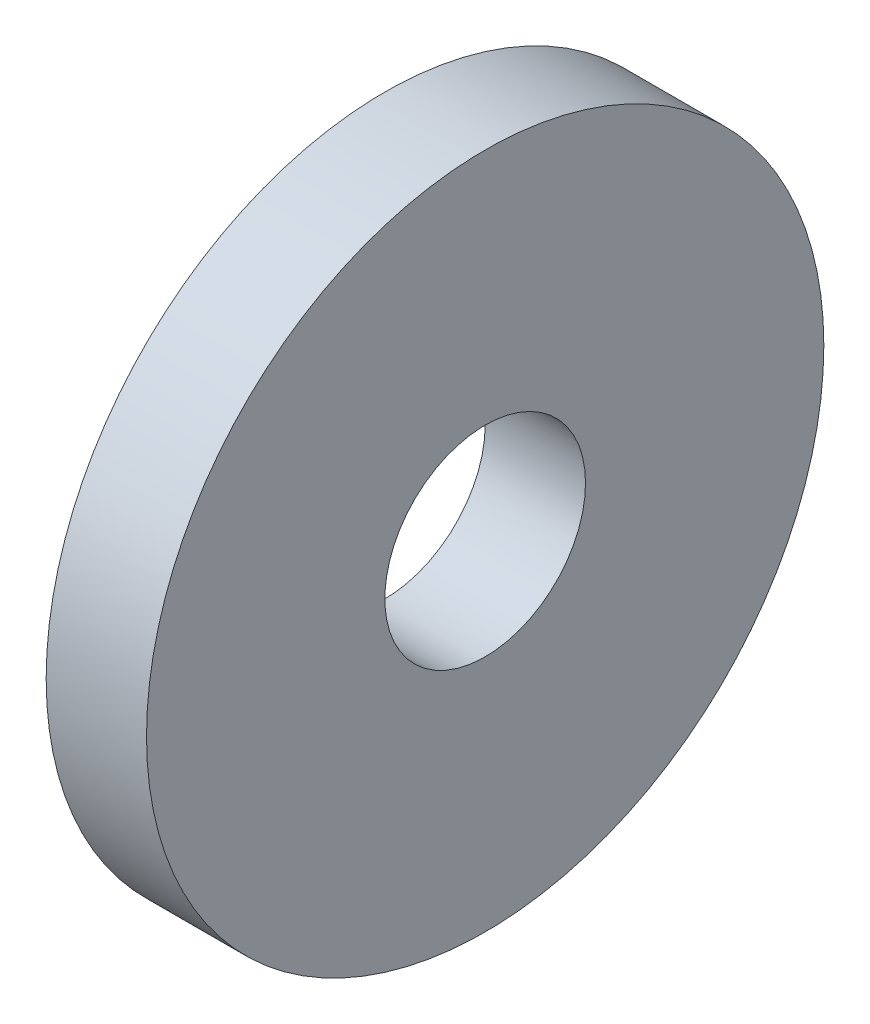
SolidWorks part; units mm, degrees
material "Pine"
ref_plane "Front Plane" through (0, 0, 0) normal (0, 0, 1) x (1, 0, 0)
ref_plane "Top Plane" through (0, 0, 0) normal (0, 1, 0) x (1, 0, 0)
ref_plane "Right Plane" through (0, 0, 0) normal (1, 0, 0) x (0, 0, -1)
sketch "Sketch1" plane through (0, 0, 0) normal (1, 0, 0) x (0, 0, -1)
  circle A0 centre (0, 0) radius 6.75
  dimension "D1" = 13.5
extrude "Boss-Extrude1" add sketch "Sketch1" along normal blind 2
sketch "Sketch2" plane through (2, 0, 0) normal (1, 0, 0) x (0, 0, -1)
  circle A0 centre (0, 0) radius 2
  dimension "D1" = 4
extrude "Cut-Extrude1" cut sketch "Sketch2" against normal through all
